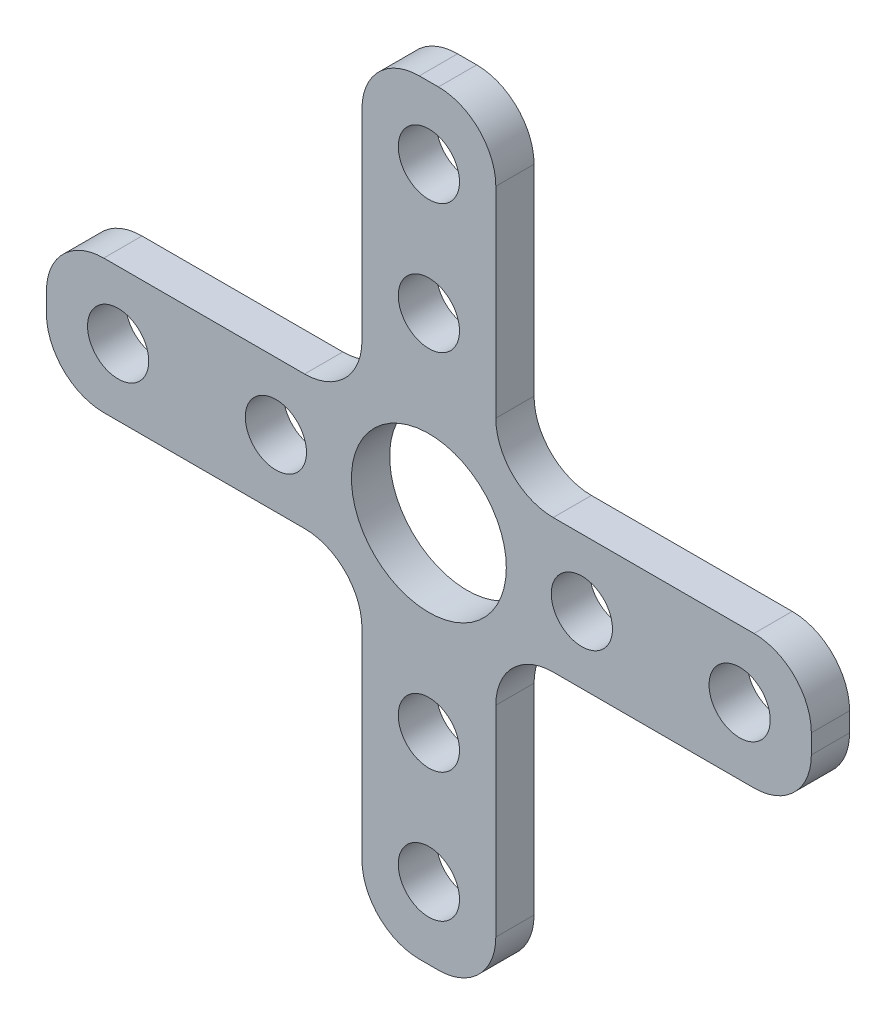
SolidWorks part; units mm, degrees
ref_plane "Alzado" through (0, 0, 0) normal (0, 0, 1) x (1, 0, 0)
ref_plane "Planta" through (0, 0, 0) normal (0, 1, 0) x (1, 0, 0)
ref_plane "Vista lateral" through (0, 0, 0) normal (1, 0, 0) x (0, 0, -1)
sketch "Croquis1" plane through (0, 0, 0) normal (0, 0, 1) x (1, 0, 0)
  line L0 (-8, 0) -> (8, 0) construction
  line L1 (0, 16.25) -> (0, -16.25) construction
  line L2 (0, -9.5) -> (0, 9.5) construction
  line L3 (-16.25, 0) -> (16.25, 0) construction
  line L4 (3.5, -3.5) -> (20, -3.5)
  line L5 (-3.5, 20) -> (3.5, 20)
  line L6 (-3.5, 20) -> (-3.5, 3.5)
  line L7 (-3.5, -20) -> (3.5, -20)
  line L8 (3.5, 20) -> (3.5, 3.5)
  line L9 (-3.5, 20) -> (3.5, -20) construction
  line L10 (-3.5, -20) -> (3.5, 20) construction
  line L11 (-20, -3.5) -> (-3.5, -3.5)
  line L12 (-20, -3.5) -> (-20, 3.5)
  line L13 (-20, 3.5) -> (-3.5, 3.5)
  line L14 (20, -3.5) -> (20, 3.5)
  line L15 (-20, -3.5) -> (20, 3.5) construction
  line L16 (-20, 3.5) -> (20, -3.5) construction
  line L17 (3.5, 3.5) -> (20, 3.5)
  line L18 (3.5, -3.5) -> (3.5, -20)
  line L19 (-3.5, -3.5) -> (-3.5, -20)
  circle A0 centre (-8, 0) radius 1.6
  circle A1 centre (8, 0) radius 1.6
  circle A2 centre (0, 16.25) radius 1.6
  circle A3 centre (0, -16.25) radius 1.6
  circle A4 centre (0, 0) radius 4.05
  circle A5 centre (0, 9.5) radius 1.6
  circle A6 centre (0, -9.5) radius 1.6
  circle A7 centre (-16.25, 0) radius 1.6
  circle A8 centre (16.25, 0) radius 1.6
  point P4 (0, 0)
  point P9 (0, 0)
  point P20 (0, 0)
  point P23 (0, 0)
  dimension "D2" = 3.2
  dimension "D3" = 8.1
  dimension "D1" = 16
  dimension "D4" = 32.5
  dimension "D5" = 19
  dimension "D6" = 32.5
  dimension "D7" = 7
  dimension "D8" = 7
  dimension "D9" = 40
  dimension "D10" = 40
  dimension "D11" = 7
extrude "Saliente-Extruir1" add sketch "Croquis1" along normal mid plane 2
fillet "Redondeo1" radius 3 12 edges at (-3.5, 3.5, 0) (-3.5, -3.5, 0) (-3.5, -20, 0) (3.5, -20, 0) (3.5, -3.5, 0) (20, -3.5, 0) (20, 3.5, 0) (3.5, 3.5, 0) (3.5, 20, 0) (-3.5, 20, 0) (-20, 3.5, 0) (-20, -3.5, 0)
